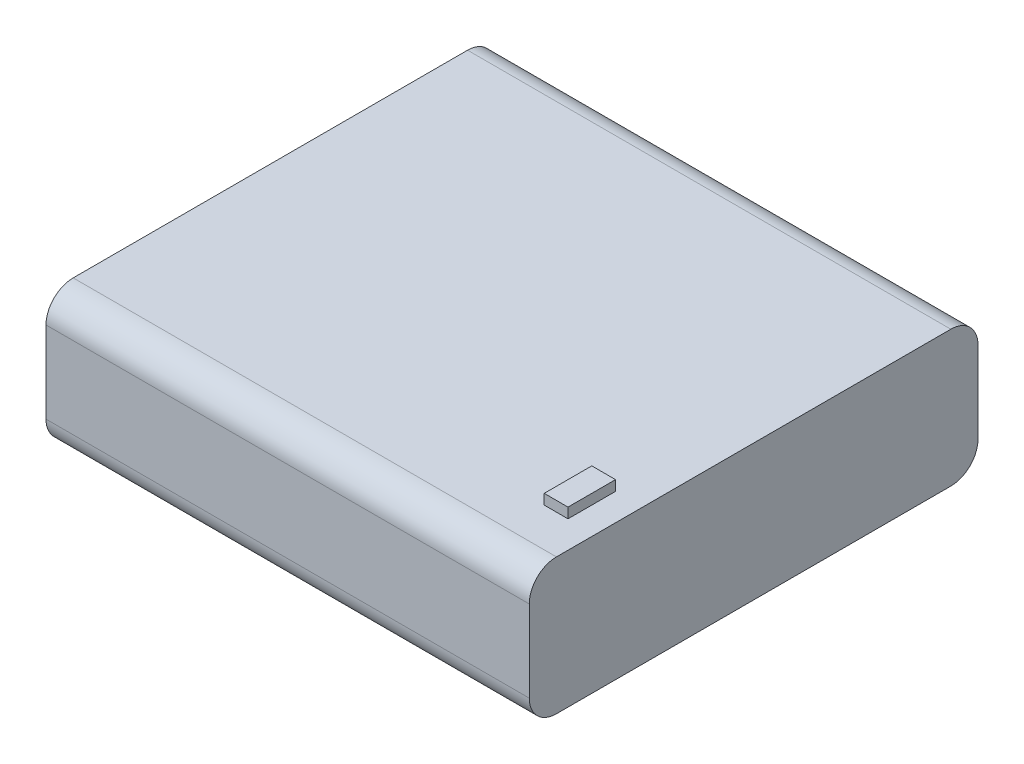
SolidWorks part; units mm, degrees
material "ABS"
ref_plane "Front" through (0, 0, 0) normal (0, 0, 1) x (1, 0, 0)
ref_plane "Top" through (0, 0, 0) normal (0, 1, 0) x (1, 0, 0)
ref_plane "Right" through (0, 0, 0) normal (1, 0, 0) x (0, 0, -1)
sketch "Sketch1" plane through (0, 0, 0) normal (0, 1, 0) x (1, 0, 0)
  line L1 (-35.56, 33.02) -> (35.56, 33.02)
  line L2 (-35.56, 33.02) -> (-35.56, -33.02)
  line L3 (-35.56, -33.02) -> (35.56, -33.02)
  line L4 (35.56, 33.02) -> (35.56, -33.02)
  line L5 (-35.56, 33.02) -> (35.56, -33.02) construction
  line L6 (-35.56, -33.02) -> (35.56, 33.02) construction
  point P0 (0, 0)
  dimension "D1" = 71.12
  dimension "D2" = 66.04
extrude "Boss-Extrude1" add sketch "Sketch1" along normal blind 20
fillet "Fillet1" radius 4 4 edges at (0, 0, -33.02) (0, 20, -33.02) (0, 0, 33.02) (0, 20, 33.02)
sketch "Sketch2" plane through (0, 20, 0) normal (0, 1, 0) x (1, 0, 0)
  line L0 (35.56, -33.02) -> (-35.56, -33.02) construction
  line L1 (28.06, -16.32) -> (31.56, -16.32)
  line L2 (28.06, -16.32) -> (28.06, -23.32)
  line L3 (28.06, -23.32) -> (31.56, -23.32)
  line L4 (31.56, -16.32) -> (31.56, -23.32)
  line L5 (28.06, -16.32) -> (31.56, -23.32) construction
  line L6 (28.06, -23.32) -> (31.56, -16.32) construction
  line L7 (35.56, -29.02) -> (35.56, 29.02) construction
  point P0 (29.81, -19.82)
  dimension "D1" = 3.5
  dimension "D2" = 7
  dimension "D3" = 9.7
  dimension "D4" = 4
extrude "Boss-Extrude2" add sketch "Sketch2" along normal blind 1.5 contours L2 L3 L4 L1
